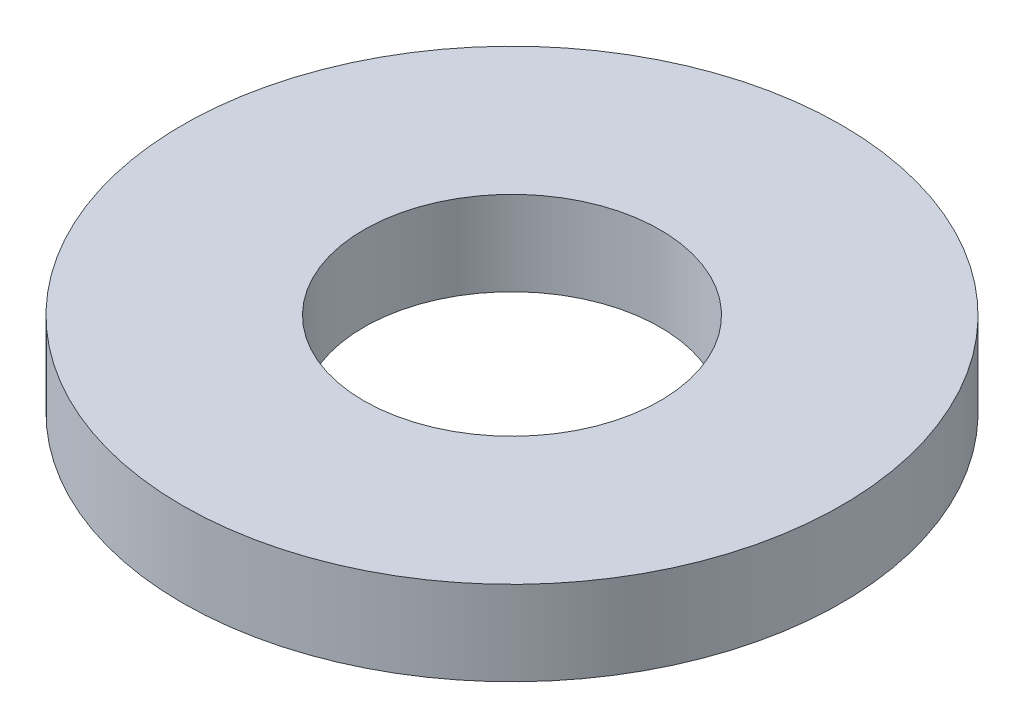
SolidWorks part; units mm, degrees
ref_plane "Front Plane" through (0, 0, 0) normal (0, 0, 1) x (1, 0, 0)
ref_plane "Top Plane" through (0, 0, 0) normal (0, 1, 0) x (1, 0, 0)
ref_plane "Right Plane" through (0, 0, 0) normal (1, 0, 0) x (0, 0, -1)
sketch "Sketch1" plane through (0, 0, 0) normal (0, 1, 0) x (1, 0, 0)
  circle A0 centre (0, 0) radius 7.9375
  dimension "OD" = 15.875
extrude "Boss-Extrude1" add sketch "Sketch1" along normal blind 2.032
sketch "Sketch5" plane through (0, 2.032, 0) normal (0, 1, 0) x (-1, 0, 0)
  circle A0 centre (0, 0) radius 3.5687
  dimension "ID" = 7.1374
extrude "Cut-Extrude1" cut sketch "Sketch5" against normal through all
